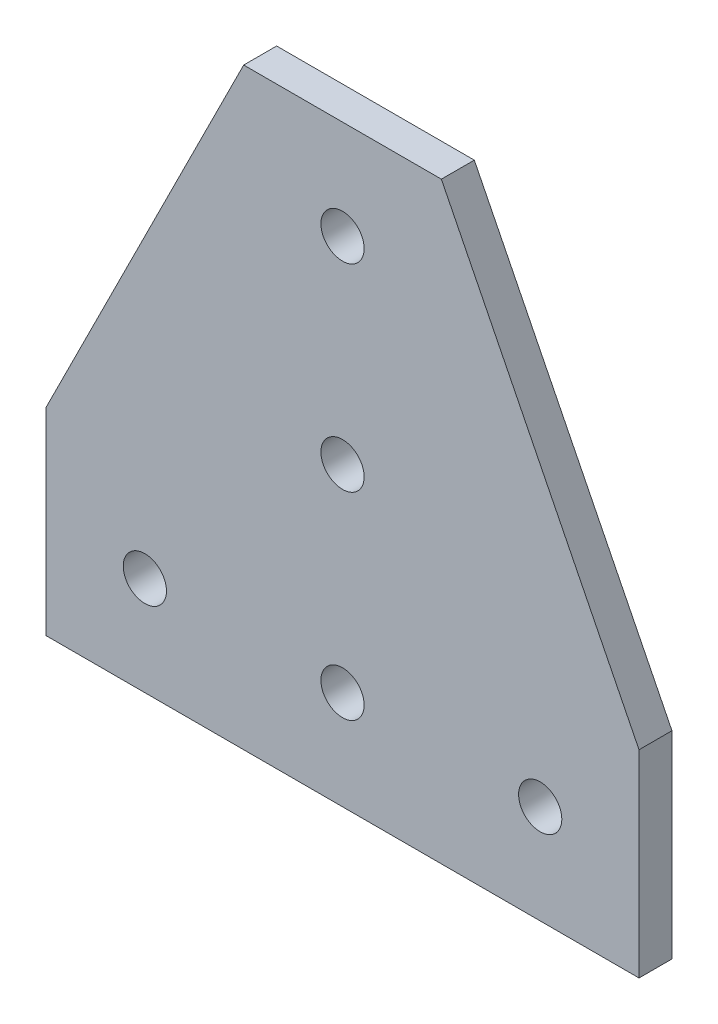
SolidWorks part; units mm, degrees
ref_plane "Front Plane" through (0, 0, 0) normal (0, 0, 1) x (1, 0, 0)
ref_plane "Top Plane" through (0, 0, 0) normal (0, 1, 0) x (1, 0, 0)
ref_plane "Right Plane" through (0, 0, 0) normal (1, 0, 0) x (0, 0, -1)
sketch "Sketch1" plane through (0, 0, 0) normal (0, 0, 1) x (1, 0, 0)
  line L0 (0, 0) -> (0, 38.1)
  line L1 (19.05, 19.05) -> (57.15, 19.05) construction
  line L2 (57.15, 19.05) -> (95.25, 19.05) construction
  line L3 (57.15, 95.25) -> (57.15, 114.3) construction
  line L4 (114.3, 38.1) -> (76.2, 114.3)
  line L5 (114.3, 0) -> (0, 0)
  line L6 (57.15, 57.15) -> (57.15, 95.25) construction
  line L7 (114.3, 38.1) -> (114.3, 0)
  line L8 (38.1, 114.3) -> (76.2, 114.3)
  line L9 (0, 38.1) -> (38.1, 114.3)
  line L11 (57.15, 19.05) -> (57.15, 57.15) construction
  circle A0 centre (19.05, 19.05) radius 4.1656
  circle A1 centre (57.15, 19.05) radius 4.1656
  circle A2 centre (95.25, 19.05) radius 4.1656
  circle A3 centre (57.15, 57.15) radius 4.1656
  circle A4 centre (57.15, 95.25) radius 4.1656
  dimension "D1" = 38.1
  dimension "E" = 8.3312
  dimension "D2" = 19.05
  dimension "D3" = 19.05
  dimension "B1" = 114.3
  dimension "C1" = 38.1
  dimension "C2" = 38.1
  dimension "B2" = 114.3
extrude "Boss-Extrude1" add sketch "Sketch1" along normal mid plane 6.35
